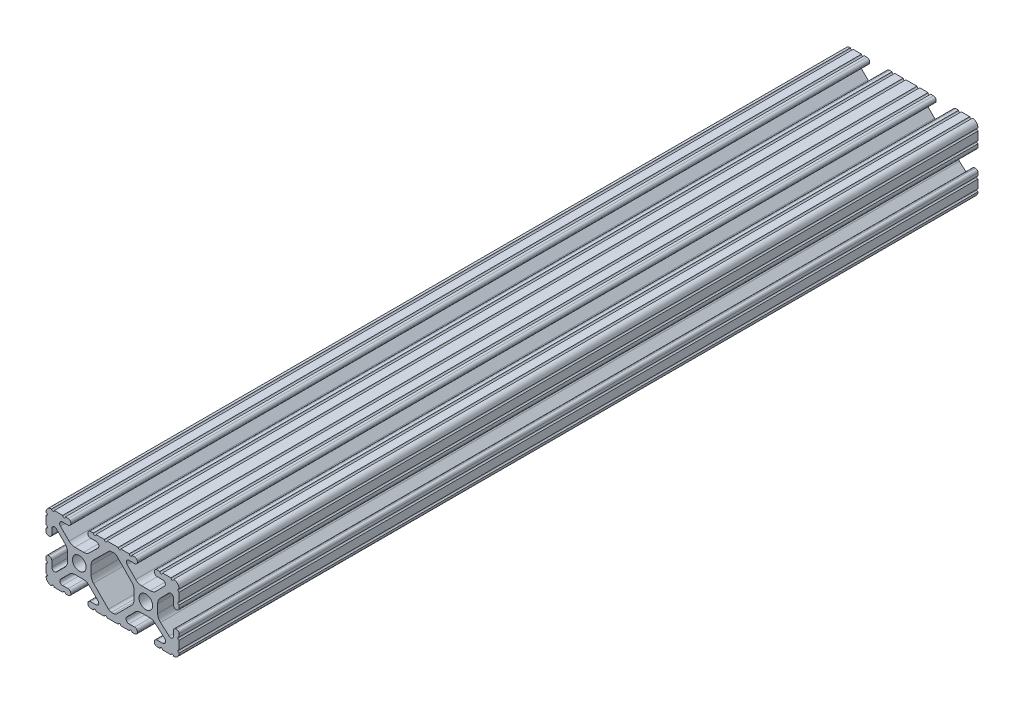
SolidWorks part; units mm, degrees
ref_plane "Front Plane" through (0, 0, 0) normal (0, 0, 1) x (1, 0, 0)
ref_plane "Top Plane" through (0, 0, 0) normal (0, 1, 0) x (1, 0, 0)
ref_plane "Right Plane" through (0, 0, 0) normal (1, 0, 0) x (0, 0, -1)
sketch "Sketch1" plane through (0, 0, 0) normal (0, 0, 1) x (1, 0, 0)
  line L0 (-7.2595, -3.8694) -> (-1.5457, -9.5728)
  line L1 (-8.1915, 1.6223) -> (-8.1915, -1.6223)
  line L2 (-1.504, 9.5765) -> (-7.252, 3.8768)
  line L3 (0.5515, 10.033) -> (-0.3952, 10.033)
  line L4 (7.2829, 3.8459) -> (1.6756, 9.5611)
  line L5 (8.1915, -1.6223) -> (8.1915, 1.6223)
  line L6 (1.5457, -9.5728) -> (7.2595, -3.8694)
  line L7 (-0.4332, -10.033) -> (0.4332, -10.033)
  line L8 (18.0171, 12.7) -> (16.9875, 12.7)
  line L9 (15.9385, 11.651) -> (15.9385, 11.5392)
  line L10 (16.9875, 10.4902) -> (19.1164, 10.4902)
  line L11 (19.8441, 8.7652) -> (16.619, 5.4551)
  line L12 (14.3449, 4.4958) -> (11.0833, 4.4958)
  line L13 (8.817, 5.4472) -> (5.5642, 8.7627)
  line L14 (6.2894, 10.4902) -> (8.4125, 10.4902)
  line L15 (9.4615, 11.5392) -> (9.4615, 11.651)
  line L16 (8.4125, 12.7) -> (7.3829, 12.7)
  line L17 (6.3669, 12.7) -> (3.1496, 12.7)
  line L18 (2.1336, 12.7) -> (-2.1336, 12.7)
  line L19 (-3.1496, 12.7) -> (-6.3669, 12.7)
  line L20 (-7.3829, 12.7) -> (-8.4125, 12.7)
  line L21 (-9.4615, 11.651) -> (-9.4615, 11.5392)
  line L22 (-8.4125, 10.4902) -> (-6.2836, 10.4902)
  line L23 (-5.5326, 8.6661) -> (-8.81, 5.4163)
  line L24 (-11.0455, 4.4958) -> (-14.3545, 4.4958)
  line L25 (-16.59, 5.4163) -> (-19.8674, 8.6661)
  line L26 (-19.1164, 10.4902) -> (-16.9875, 10.4902)
  line L27 (-15.9385, 11.5392) -> (-15.9385, 11.651)
  line L28 (-16.9875, 12.7) -> (-18.0171, 12.7)
  line L29 (-19.0331, 12.7) -> (-22.2504, 12.7)
  line L30 (-25.4, 9.5504) -> (-25.4, 6.3331)
  line L31 (-25.4, 5.3171) -> (-25.4, 4.2375)
  line L32 (-24.401, 3.2385) -> (-24.2392, 3.2385)
  line L33 (-23.1902, 4.2875) -> (-23.1902, 6.3347)
  line L34 (-21.434, 7.0665) -> (-18.148, 3.8082)
  line L35 (-17.2085, 1.5536) -> (-17.2085, -1.6952)
  line L36 (-18.1405, -3.9423) -> (-21.4316, -7.2274)
  line L37 (-23.1902, -6.498) -> (-23.1902, -4.2875)
  line L38 (-24.2392, -3.2385) -> (-24.351, -3.2385)
  line L39 (-25.4, -4.2875) -> (-25.4, -5.3171)
  line L40 (-25.4, -6.3331) -> (-25.4, -9.5504)
  line L41 (-22.2504, -12.7) -> (-19.0331, -12.7)
  line L42 (-18.0171, -12.7) -> (-16.9875, -12.7)
  line L43 (-15.9384, -11.651) -> (-15.9384, -11.5392)
  line L44 (-16.9875, -10.4902) -> (-19.1164, -10.4902)
  line L45 (-19.8341, -8.7551) -> (-16.4966, -5.4237)
  line L46 (-14.2536, -4.4958) -> (-11.1464, -4.4958)
  line L47 (-8.9034, -5.4237) -> (-5.5659, -8.7551)
  line L48 (-6.2836, -10.4902) -> (-8.4125, -10.4902)
  line L49 (-9.4616, -11.5392) -> (-9.4616, -11.651)
  line L50 (-8.4125, -12.7) -> (-7.3829, -12.7)
  line L51 (-6.3669, -12.7) -> (-3.1496, -12.7)
  line L52 (-2.1336, -12.7) -> (2.1336, -12.7)
  line L53 (3.1496, -12.7) -> (6.3669, -12.7)
  line L54 (7.3829, -12.7) -> (8.4125, -12.7)
  line L55 (9.4616, -11.651) -> (9.4616, -11.5392)
  line L56 (8.4125, -10.4902) -> (6.2894, -10.4902)
  line L57 (5.4807, -8.5353) -> (8.5979, -5.4237)
  line L58 (10.8409, -4.4958) -> (14.1026, -4.4958)
  line L59 (16.1879, -5.2766) -> (19.8682, -8.4822)
  line L60 (19.1164, -10.4902) -> (16.9875, -10.4902)
  line L61 (15.9384, -11.5392) -> (15.9384, -11.651)
  line L62 (16.9875, -12.7) -> (18.0171, -12.7)
  line L63 (19.0331, -12.7) -> (22.2504, -12.7)
  line L64 (25.4, -9.5504) -> (25.4, -6.3331)
  line L65 (25.4, -5.3171) -> (25.4, -4.2375)
  line L66 (24.401, -3.2385) -> (24.1892, -3.2385)
  line L67 (23.1902, -4.2375) -> (23.1902, -6.1559)
  line L68 (21.584, -6.8869) -> (18.2982, -4.025)
  line L69 (17.2085, -1.6308) -> (17.2085, 1.6308)
  line L70 (18.1094, 3.8465) -> (21.5263, 7.3534)
  line L71 (23.1902, 6.6769) -> (23.1902, 4.2375)
  line L72 (24.1892, 3.2385) -> (24.401, 3.2385)
  line L73 (25.4, 4.2375) -> (25.4, 5.3171)
  line L74 (25.4, 6.3332) -> (25.4, 9.5504)
  line L75 (22.2504, 12.7) -> (19.0331, 12.7)
  circle A0 centre (-12.7, 0) radius 2.6035
  circle A1 centre (12.7, 0) radius 2.6035
  arc A2 (-1.5457, -9.5728) -> (-0.4332, -10.033) centre (-0.4332, -8.4582) ccw
  arc A3 (-8.1915, -1.6223) -> (-7.2595, -3.8694) centre (-5.0165, -1.6223) ccw
  arc A4 (-7.252, 3.8768) -> (-8.1915, 1.6223) centre (-5.0165, 1.6223) ccw
  arc A5 (-0.3952, 10.033) -> (-1.504, 9.5765) centre (-0.3952, 8.4582) ccw
  arc A6 (1.6756, 9.5611) -> (0.5515, 10.033) centre (0.5515, 8.4582) ccw
  arc A7 (8.1915, 1.6223) -> (7.2829, 3.8459) centre (5.0165, 1.6223) ccw
  arc A8 (7.2595, -3.8694) -> (8.1915, -1.6223) centre (5.0165, -1.6223) ccw
  arc A9 (0.4332, -10.033) -> (1.5457, -9.5728) centre (0.4332, -8.4582) ccw
  arc A10 (18.0171, 12.7) -> (19.0331, 12.7) centre (18.5251, 12.7) ccw
  arc A11 (16.9875, 12.7) -> (15.9385, 11.651) centre (16.9875, 11.651) ccw
  arc A12 (15.9385, 11.5392) -> (16.9875, 10.4902) centre (16.9875, 11.5392) ccw
  arc A13 (19.8441, 8.7652) -> (19.1164, 10.4902) centre (19.1164, 9.4742) ccw
  arc A14 (14.3449, 4.4958) -> (16.619, 5.4551) centre (14.3449, 7.6708) ccw
  arc A15 (8.817, 5.4472) -> (11.0833, 4.4958) centre (11.0833, 7.6708) ccw
  arc A16 (6.2894, 10.4902) -> (5.5642, 8.7627) centre (6.2894, 9.4742) ccw
  arc A17 (8.4125, 10.4902) -> (9.4615, 11.5392) centre (8.4125, 11.5392) ccw
  arc A18 (9.4615, 11.651) -> (8.4125, 12.7) centre (8.4125, 11.651) ccw
  arc A19 (6.3669, 12.7) -> (7.3829, 12.7) centre (6.8749, 12.7) ccw
  arc A20 (2.1336, 12.7) -> (3.1496, 12.7) centre (2.6416, 12.7) ccw
  arc A21 (-3.1496, 12.7) -> (-2.1336, 12.7) centre (-2.6416, 12.7) ccw
  arc A22 (-7.3829, 12.7) -> (-6.3669, 12.7) centre (-6.8749, 12.7) ccw
  arc A23 (-8.4125, 12.7) -> (-9.4615, 11.651) centre (-8.4125, 11.651) ccw
  arc A24 (-9.4615, 11.5392) -> (-8.4125, 10.4902) centre (-8.4125, 11.5392) ccw
  arc A25 (-5.5326, 8.6661) -> (-6.2836, 10.4902) centre (-6.2836, 9.4235) ccw
  arc A26 (-11.0455, 4.4958) -> (-8.81, 5.4163) centre (-11.0455, 7.6708) ccw
  arc A27 (-16.59, 5.4163) -> (-14.3545, 4.4958) centre (-14.3545, 7.6708) ccw
  arc A28 (-19.1164, 10.4902) -> (-19.8674, 8.6661) centre (-19.1164, 9.4235) ccw
  arc A29 (-16.9875, 10.4902) -> (-15.9385, 11.5392) centre (-16.9875, 11.5392) ccw
  arc A30 (-15.9385, 11.651) -> (-16.9875, 12.7) centre (-16.9875, 11.651) ccw
  arc A31 (-19.0331, 12.7) -> (-18.0171, 12.7) centre (-18.5251, 12.7) ccw
  arc A32 (-23.2664, 12.6998) -> (-22.2504, 12.7) centre (-22.7584, 12.7) ccw
  arc A33 (-23.2664, 12.6998) -> (-25.3998, 10.5664) centre (-23.2918, 10.5918) ccw
  arc A34 (-25.4, 9.5504) -> (-25.3998, 10.5664) centre (-25.4, 10.0584) ccw
  arc A35 (-25.4, 5.3171) -> (-25.4, 6.3331) centre (-25.4, 5.8251) ccw
  arc A36 (-25.4, 4.2375) -> (-24.401, 3.2385) centre (-24.401, 4.2375) ccw
  arc A37 (-24.2392, 3.2385) -> (-23.1902, 4.2875) centre (-24.2392, 4.2875) ccw
  arc A38 (-21.434, 7.0665) -> (-23.1902, 6.3347) centre (-22.1596, 6.3347) ccw
  arc A39 (-17.2085, 1.5536) -> (-18.148, 3.8082) centre (-20.3835, 1.5536) ccw
  arc A40 (-18.1405, -3.9423) -> (-17.2085, -1.6952) centre (-20.3835, -1.6952) ccw
  arc A41 (-23.1902, -6.498) -> (-21.4316, -7.2274) centre (-22.1596, -6.498) ccw
  arc A42 (-23.1902, -4.2875) -> (-24.2392, -3.2385) centre (-24.2392, -4.2875) ccw
  arc A43 (-24.351, -3.2385) -> (-25.4, -4.2875) centre (-24.351, -4.2875) ccw
  arc A44 (-25.4, -6.3331) -> (-25.4, -5.3171) centre (-25.4, -5.8251) ccw
  arc A45 (-25.3998, -10.5664) -> (-25.4, -9.5504) centre (-25.4, -10.0584) ccw
  arc A46 (-25.3998, -10.5664) -> (-23.2664, -12.6998) centre (-23.2918, -10.5918) ccw
  arc A47 (-22.2504, -12.7) -> (-23.2664, -12.6998) centre (-22.7584, -12.7) ccw
  arc A48 (-18.0171, -12.7) -> (-19.0331, -12.7) centre (-18.5251, -12.7) ccw
  arc A49 (-16.9875, -12.7) -> (-15.9384, -11.651) centre (-16.9875, -11.651) ccw
  arc A50 (-15.9384, -11.5392) -> (-16.9875, -10.4902) centre (-16.9875, -11.5392) ccw
  arc A51 (-19.8341, -8.7551) -> (-19.1164, -10.4902) centre (-19.1164, -9.4742) ccw
  arc A52 (-14.2536, -4.4958) -> (-16.4966, -5.4237) centre (-14.2536, -7.6708) ccw
  arc A53 (-8.9034, -5.4237) -> (-11.1464, -4.4958) centre (-11.1464, -7.6708) ccw
  arc A54 (-6.2836, -10.4902) -> (-5.5659, -8.7551) centre (-6.2836, -9.4742) ccw
  arc A55 (-8.4125, -10.4902) -> (-9.4616, -11.5392) centre (-8.4125, -11.5392) ccw
  arc A56 (-9.4616, -11.651) -> (-8.4125, -12.7) centre (-8.4125, -11.651) ccw
  arc A57 (-6.3669, -12.7) -> (-7.3829, -12.7) centre (-6.8749, -12.7) ccw
  arc A58 (-2.1336, -12.7) -> (-3.1496, -12.7) centre (-2.6416, -12.7) ccw
  arc A59 (3.1496, -12.7) -> (2.1336, -12.7) centre (2.6416, -12.7) ccw
  arc A60 (7.3829, -12.7) -> (6.3669, -12.7) centre (6.8749, -12.7) ccw
  arc A61 (8.4125, -12.7) -> (9.4616, -11.651) centre (8.4125, -11.651) ccw
  arc A62 (9.4616, -11.5392) -> (8.4125, -10.4902) centre (8.4125, -11.5392) ccw
  arc A63 (5.4807, -8.5353) -> (6.2894, -10.4902) centre (6.2894, -9.3455) ccw
  arc A64 (10.8409, -4.4958) -> (8.5979, -5.4237) centre (10.8409, -7.6708) ccw
  arc A65 (16.1879, -5.2766) -> (14.1026, -4.4958) centre (14.1026, -7.6708) ccw
  arc A66 (19.1164, -10.4902) -> (19.8682, -8.4822) centre (19.1164, -9.3455) ccw
  arc A67 (16.9875, -10.4902) -> (15.9384, -11.5392) centre (16.9875, -11.5392) ccw
  arc A68 (15.9384, -11.651) -> (16.9875, -12.7) centre (16.9875, -11.651) ccw
  arc A69 (19.0331, -12.7) -> (18.0171, -12.7) centre (18.5251, -12.7) ccw
  arc A70 (23.2664, -12.6998) -> (22.2504, -12.7) centre (22.7584, -12.7) ccw
  arc A71 (23.2664, -12.6998) -> (25.3998, -10.5664) centre (23.2918, -10.5918) ccw
  arc A72 (25.4, -9.5504) -> (25.3998, -10.5664) centre (25.4, -10.0584) ccw
  arc A73 (25.4, -5.3171) -> (25.4, -6.3331) centre (25.4, -5.8251) ccw
  arc A74 (25.4, -4.2375) -> (24.401, -3.2385) centre (24.401, -4.2375) ccw
  arc A75 (24.1892, -3.2385) -> (23.1902, -4.2375) centre (24.1892, -4.2375) ccw
  arc A76 (21.584, -6.8869) -> (23.1902, -6.1559) centre (22.2207, -6.1559) ccw
  arc A77 (17.2085, -1.6308) -> (18.2982, -4.025) centre (20.3835, -1.6308) ccw
  arc A78 (18.1094, 3.8465) -> (17.2085, 1.6308) centre (20.3835, 1.6308) ccw
  arc A79 (23.1902, 6.6769) -> (21.5263, 7.3534) centre (22.2207, 6.6769) ccw
  arc A80 (23.1902, 4.2375) -> (24.1892, 3.2385) centre (24.1892, 4.2375) ccw
  arc A81 (24.401, 3.2385) -> (25.4, 4.2375) centre (24.401, 4.2375) ccw
  arc A82 (25.4, 6.3332) -> (25.4, 5.3171) centre (25.4, 5.8251) ccw
  arc A83 (25.3998, 10.5664) -> (25.4, 9.5504) centre (25.4, 10.0584) ccw
  arc A84 (25.3998, 10.5664) -> (23.2664, 12.6998) centre (23.2918, 10.5918) ccw
  arc A85 (22.2504, 12.7) -> (23.2664, 12.6998) centre (22.7584, 12.7) ccw
  point P248 (0, 10.033)
extrude "Boss-Extrude1" add sketch "Sketch1" along normal mid plane 304.8
